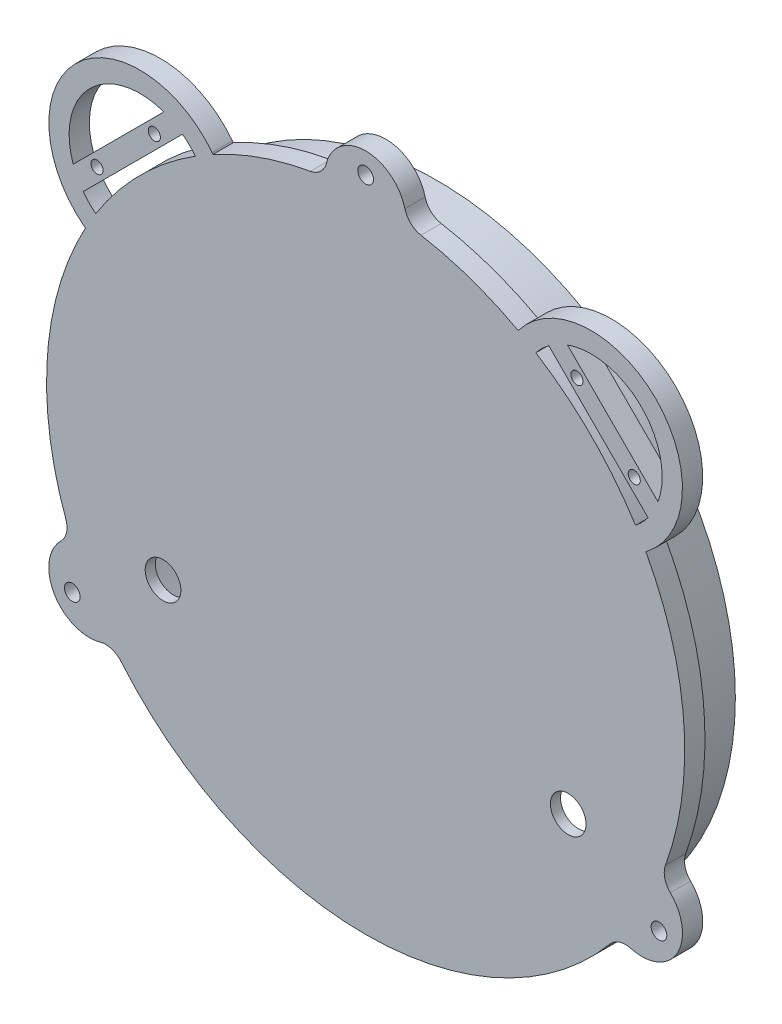
SolidWorks part; units mm, degrees
material "6061 Alloy"
ref_plane "Front Plane" through (0, 0, 0) normal (0, 0, 1) x (1, 0, 0)
ref_plane "Top Plane" through (0, 0, 0) normal (0, 1, 0) x (1, 0, 0)
ref_plane "Right Plane" through (0, 0, 0) normal (1, 0, 0) x (0, 0, -1)
sketch "Sketch1" plane through (0, 0, 0) normal (0, 0, 1) x (1, 0, 0)
  circle A0 centre (0, 0) radius 100.0125
extrude "Extrude1" add sketch "Sketch1" along normal blind 6.35
sketch "Sketch2" plane through (0, 0, 0) normal (0, 0, -1) x (-1, 0, 0)
  circle A0 centre (0, 0) radius 93.6625
extrude "Extrude2" add sketch "Sketch2" along normal blind 15.875
sketch "Sketch3" plane through (0, 0, -15.875) normal (0, 0, -1) x (-1, 0, 0)
  circle A0 centre (0, 0) radius 87.3125
extrude "Cut-Extrude1" cut sketch "Sketch3" against normal blind 19.05
sketch "Sketch5" plane through (0, 0, 6.35) normal (0, 0, 1) x (1, 0, 0)
  circle A18 centre (-63.5, -35.56) radius 5.588
  circle A19 centre (63.5, -35.56) radius 5.588
  dimension "D1" = 63.5
  dimension "D5" = 35.56
  dimension "D2" = 63.5
  dimension "D6" = 35.56
sketch "Sketch7" plane through (0, 0, 6.35) normal (0, 0, 1) x (1, 0, 0)
  line L0 (0, 0) -> (0, 100.0125) construction
  circle A0 centre (0, 0) radius 100.0125 construction
sketch "Sketch8" plane through (0, 0, 6.35) normal (0, 0, 1) x (1, 0, 0)
  line L0 (0, 0) -> (86.6134, -50.0063) construction
  line L1 (0, 0) -> (-86.6134, -50.0063) construction
  line L2 (0, 0) -> (0, 100.0125) construction
  circle A0 centre (0, 0) radius 100.0125 construction
  arc A1 (-12.6744, 99.2062) -> (12.6744, 99.2062) centre (0, 100.0125) cw
  arc A2 (92.2522, -38.6267) -> (79.5779, -60.5794) centre (86.6134, -50.0063) cw
  arc A3 (-92.2522, -38.6267) -> (-79.5779, -60.5794) centre (-86.6134, -50.0063) ccw
  arc A4 (-12.6744, 99.2062) -> (12.6744, 99.2062) centre (0, 0) cw
  arc A5 (92.2522, -38.6267) -> (79.5779, -60.5794) centre (0, 0) cw
  arc A6 (-92.2522, -38.6267) -> (-79.5779, -60.5794) centre (0, 0) ccw
  dimension "D1" = 12.7
  dimension "D2" = 12.7
  dimension "D3" = 12.7
  dimension "D4" = 120
  dimension "D5" = 120
extrude "Extrude3" add sketch "Sketch8" against normal up to surface (6.35 mm away) up to face at (100.0125, 0, 0)
sketch "Sketch10" plane through (0, 0, 6.35) normal (0, 0, 1) x (1, 0, 0)
  line L0 (0, 0) -> (0, 123.4907) construction
  line L1 (0, 0) -> (137.3268, -79.2857) construction
  line L2 (0, 0) -> (-146.5837, -84.6301) construction
extrude "Cut-Extrude2" cut sketch "Sketch5" against normal through all
hole_wizard "#10 (0.1935) Diameter Hole1" positions "3DSketch2" profile "Sketch11" hole size "#10" standard "Ansi Inch"
sketch3d "3DSketch2"
  line L0 (0, 0, 6.35) -> (0, 123.4907, 6.35) construction
  line L1 (0, 0, 6.35) -> (137.3268, -79.2857, 6.35) construction
  line L2 (0, 0, 6.35) -> (-146.5837, -84.6301, 6.35) construction
  point P0 (0, 106.1728, 6.35)
  point P4 (91.9483, -53.0864, 6.35)
  point P8 (-91.9483, -53.0864, 6.35)
  dimension "D1" = 106.3625
  dimension "D2" = 106.3625
  dimension "D3" = 106.3625
sketch "Sketch11" plane through (0, 106.1728, 6.35) normal (1, 0, 0) x (0, -1, 0)
  line L0 (0, 0) -> (0, 331.6766)
  line L1 (0, 331.6766) -> (2.4574, 330.2)
  line L2 (2.4574, 330.2) -> (2.4574, 0)
  line L5 (2.4574, 0) -> (0, 0)
  line L10 (0, 331.6766) -> (-2.4575, 330.2) construction
  line L11 (0, -6.35) -> (0, 107.95) construction
  dimension "Hole Dia." = 4.9149
  dimension "Hole Depth" = 330.2
  dimension "Drill Angle" = 118
hole_wizard "1/8 NPT Tapped Hole1"
sketch3d "3DSketch6"
  line L0 (0, 0, 0) -> (87.3125, 0, 0) construction
  line L2 (0, 0, 0) -> (0, 87.3125, 0) construction
  circle A0 centre (0, 0, 3.175) radius 87.3125 construction
  point P3 (-50.7007, 50.7007, 3.175)
  point P10 (0, 0, -84.1375)
  dimension "D1" = 50.8
  dimension "D2" = 50.8
sketch "Sketch16" plane through (-50.7007, 50.7007, 3.175) normal (1, 0, 0) x (0, 1, 0)
  line L0 (0, 0) -> (0, 13.7095)
  line L1 (4.2164, 11.176) -> (0, 13.7095)
  line L2 (-4.2164, 11.176) -> (0, 13.7095) construction
  line L3 (4.2164, 11.176) -> (4.2164, 6.35)
  line L4 (4.2164, 6.35) -> (4.9362, 6.35)
  line L5 (4.9362, 6.35) -> (5.1263, 0)
  line L6 (-4.9362, 6.35) -> (-5.1263, 0) construction
  line L7 (5.1263, 0) -> (0, 0)
  line L8 (0, -6.35) -> (0, 107.95) construction
  line L11 (-4.2164, 6.35) -> (-4.9362, 6.35) construction
  dimension "Tap Drill Dia." = 8.4328
  dimension "Tap Drill Depth" = 11.176
  dimension "Thread Dia." = 10.2526
  dimension "Thread Angle" = 3.43
  dimension "Thread Depth" = 6.35
  dimension "Drill Angle" = 118
fillet "Fillet1" radius 6.35 6 edges at (92.2522, -38.6267, 3.175) (79.5779, -60.5794, 3.175) (-12.6744, 99.2062, 3.175) (12.6744, 99.2062, 3.175) (-79.5779, -60.5794, 3.175) (-92.2522, -38.6267, 3.175)
sketch "Sketch22" plane through (0, 0, 6.35) normal (0, 0, 1) x (1, 0, 0)
  line L0 (0, 0) -> (0, 100.0125) construction
  line L1 (-79.302, 60.94) -> (-70.3475, 69.946)
  line L2 (-70.9217, 70.5168) -> (0, 0) construction
  line L3 (0, 0) -> (-96.8054, -25.1239) construction
  line L4 (-70.3475, 69.946) -> (-61.393, 78.9519)
  line L5 (-99.2121, -12.6278) -> (-96.0218, -24.9205)
  line L6 (-96.0218, -24.9205) -> (-92.8314, -37.2133)
  line L7 (-79.302, 60.94) -> (-84.7318, 66.3388)
  line L8 (-66.8227, 84.3506) -> (-61.393, 78.9519)
  line L9 (-84.7318, 66.3388) -> (-66.8227, 84.3506)
  line L10 (-92.8314, -37.2133) -> (-99.2121, -38.8693)
  line L11 (-99.2121, -38.8693) -> (-105.5928, -14.2838)
  line L12 (-105.5928, -14.2838) -> (-99.2121, -12.6278)
  line L13 (105.5928, -14.2838) -> (99.2121, -12.6278)
  line L14 (99.2121, -38.8693) -> (105.5928, -14.2838)
  line L15 (92.8314, -37.2133) -> (99.2121, -38.8693)
  line L16 (84.7318, 66.3388) -> (66.8227, 84.3506)
  line L17 (66.8227, 84.3506) -> (61.393, 78.9519)
  line L18 (79.302, 60.94) -> (84.7318, 66.3388)
  line L19 (96.0218, -24.9205) -> (92.8314, -37.2133)
  line L20 (99.2121, -12.6278) -> (96.0218, -24.9205)
  line L21 (70.3475, 69.946) -> (61.393, 78.9519)
  line L22 (79.302, 60.94) -> (70.3475, 69.946)
  circle A0 centre (0, 0) radius 100.0125 construction
  dimension "D1" = 45.164
  dimension "D2" = 104.549
  dimension "D3" = 25.4
  dimension "D4" = 25.4
  dimension "D5" = 12.7
  dimension "D6" = 12.7
extrude "Cut-Extrude5" [suppressed] cut sketch "Sketch22" against normal through all
hole_wizard "Tap Drill for #6 Tap2" [suppressed] positions "3DSketch11" profile "Sketch23" hole size "#6-32" standard "Ansi Inch"
sketch3d "3DSketch11" [suppressed]
  line L0 (61.393, 78.9519, 3.175) -> (79.302, 60.94, 3.175) construction
  line L1 (61.393, 78.9519, 0) -> (61.393, 78.9519, 6.35) construction
  line L2 (79.302, 60.94, 0) -> (79.302, 60.94, 6.35) construction
  line L4 (99.2121, -12.6278, 3.175) -> (92.8314, -37.2133, 3.175) construction
  line L5 (99.2121, -12.6278, 0) -> (99.2121, -12.6278, 6.35) construction
  line L6 (92.8314, -37.2133, 0) -> (92.8314, -37.2133, 6.35) construction
  line L8 (-92.8314, -37.2133, 3.175) -> (-99.2121, -12.6278, 3.175) construction
  line L9 (-92.8314, -37.2133, 0) -> (-92.8314, -37.2133, 6.35) construction
  line L10 (-99.2121, -12.6278, 0) -> (-99.2121, -12.6278, 6.35) construction
  line L12 (-61.393, 78.9519, 3.175) -> (-79.302, 60.94, 3.175) construction
  line L13 (-61.393, 78.9519, 0) -> (-61.393, 78.9519, 6.35) construction
  line L14 (-79.302, 60.94, 0) -> (-79.302, 60.94, 6.35) construction
  line L16 (-96.0218, -24.9205, 6.35) -> (-96.0218, -24.9205, 0) construction
  line L17 (-92.8314, -37.2133, 6.35) -> (-99.2121, -12.6278, 6.35) construction
  line L18 (-92.8314, -37.2133, 0) -> (-99.2121, -12.6278, 0) construction
  line L20 (-70.3475, 69.946, 6.35) -> (-70.3475, 69.946, 0) construction
  line L21 (-79.302, 60.94, 6.35) -> (-61.393, 78.9519, 6.35) construction
  line L22 (-79.302, 60.94, 0) -> (-61.393, 78.9519, 0) construction
  line L24 (70.3475, 69.946, 6.35) -> (70.3475, 69.946, 0) construction
  line L25 (61.393, 78.9519, 6.35) -> (79.302, 60.94, 6.35) construction
  line L26 (61.393, 78.9519, 0) -> (79.302, 60.94, 0) construction
  line L28 (96.0218, -24.9205, 6.35) -> (96.0218, -24.9205, 0) construction
  line L29 (99.2121, -12.6278, 6.35) -> (92.8314, -37.2133, 6.35) construction
  line L30 (99.2121, -12.6278, 0) -> (92.8314, -37.2133, 0) construction
  point P0 (-93.8284, -33.3718, 3.175)
  point P2 (-98.2151, -16.4693, 3.175)
  point P4 (-76.5038, 63.7544, 3.175)
  point P6 (-64.1913, 76.1375, 3.175)
  point P8 (64.1913, 76.1375, 3.175)
  point P10 (76.5038, 63.7544, 3.175)
  point P12 (98.2151, -16.4693, 3.175)
  point P14 (93.8284, -33.3718, 3.175)
  dimension "D1" = 17.4625
  dimension "D2" = 8.7312
  dimension "D3" = 17.4625
  dimension "D4" = 8.7312
  dimension "D5" = 17.4625
  dimension "D6" = 8.7312
  dimension "D7" = 17.4625
  dimension "D8" = 8.7312
sketch "Sketch23" plane through (-93.8284, -33.3718, 3.175) normal (0, 0, 1) x (0.2512, -0.9679, 0)
  line L0 (0, 0) -> (0, 10.3377)
  line L1 (0, 10.3377) -> (1.3525, 9.525)
  line L2 (1.3525, 9.525) -> (1.3525, 0)
  line L5 (1.3525, 0) -> (0, 0)
  line L10 (0, 10.3377) -> (-1.3526, 9.525) construction
  line L11 (0, -6.35) -> (0, 107.95) construction
  dimension "Hole Dia." = 2.7051
  dimension "Hole Depth" = 9.525
  dimension "Drill Angle" = 118
sketch "Sketch24" plane through (0, 0, 3.175) normal (0, 0, -1) x (-1, 0, 0)
  line L0 (0, 0) -> (0, 69.85) construction
  line L1 (44.45, 12.7) -> (-44.45, 12.7) construction
  line L2 (29.5275, 76.8322) -> (-29.5275, 76.8322) construction
  line L3 (29.5275, 76.8322) -> (29.5275, 62.8678) construction
  line L4 (29.5275, 62.8678) -> (-29.5275, 62.8678) construction
  line L5 (-29.5275, 76.8322) -> (-29.5275, 62.8678) construction
  line L6 (29.5275, 76.8322) -> (-29.5275, 62.8678) construction
  line L7 (29.5275, 62.8678) -> (-29.5275, 76.8322) construction
  line L8 (0, 0) -> (0, -100.0125) construction
  line L9 (-60.325, 29.5275) -> (-28.575, 29.5275) construction
  line L10 (-60.325, 29.5275) -> (-60.325, -4.1275) construction
  line L11 (-60.325, -4.1275) -> (-28.575, -4.1275) construction
  line L12 (-28.575, 29.5275) -> (-28.575, -4.1275) construction
  line L13 (-60.325, 29.5275) -> (-28.575, -4.1275) construction
  line L14 (-60.325, -4.1275) -> (-28.575, 29.5275) construction
  line L15 (-34.925, -53.975) -> (34.925, -53.975) construction
  line L16 (60.325, -4.1275) -> (28.575, 29.5275) construction
  line L17 (60.325, 29.5275) -> (28.575, -4.1275) construction
  line L18 (28.575, 29.5275) -> (28.575, -4.1275) construction
  line L19 (60.325, -4.1275) -> (28.575, -4.1275) construction
  line L20 (60.325, 29.5275) -> (60.325, -4.1275) construction
  line L21 (60.325, 29.5275) -> (28.575, 29.5275) construction
  line L22 (0, -25.4) -> (-44.45, -25.4) construction
  circle A0 centre (0, 69.85) radius 15.1765
  circle A1 centre (-60.325, -4.1275) radius 14.4145
  circle A2 centre (-28.575, 29.5275) radius 14.4145
  circle A3 centre (-28.575, -4.1275) radius 14.4145
  circle A4 centre (-60.325, 29.5275) radius 14.4145
  arc A5 (-76.6251, -64.2736) -> (76.6251, -64.2736) centre (0, 0) ccw construction
  circle A6 centre (-34.925, -53.975) radius 19.9644
  circle A7 centre (34.925, -53.975) radius 19.9644
  circle A8 centre (60.325, 29.5275) radius 14.4145
  circle A9 centre (28.575, -4.1275) radius 14.4145
  circle A10 centre (28.575, 29.5275) radius 14.4145
  circle A11 centre (60.325, -4.1275) radius 14.4145
  circle A12 centre (0, 39.6875) radius 12.827
  circle A13 centre (0, 12.7) radius 12.827
  circle A14 centre (0, -14.2875) radius 12.827
  circle A15 centre (0, -41.275) radius 12.827
  circle A16 centre (-29.5275, 62.8678) radius 12.827
  circle A17 centre (29.5275, 62.8678) radius 12.827
  circle A18 centre (0, -69.85) radius 13.6144
  circle A19 centre (-44.45, -25.4) radius 6.8542
  point P31 (0, 12.7)
  dimension "D1" = 30.353
  dimension "D4" = 28.829
  dimension "D5" = 28.829
  dimension "D6" = 28.829
  dimension "D8" = 28.829
  dimension "D11" = 39.9288
  dimension "D12" = 39.9288
  dimension "D15" = 25.654
  dimension "D17" = 25.654
  dimension "D18" = 26.9875
  dimension "D19" = 25.654
  dimension "D21" = 25.654
  dimension "D23" = 25.654
  dimension "D25" = 25.654
  dimension "D26" = 27.2288
  dimension "D27" = 28.575
  dimension "D29" = 13.7084
  dimension "D2" = 69.85
  dimension "D3" = 44.45
  dimension "D7" = 31.75
  dimension "D9" = 12.7
  dimension "D10" = 33.655
  dimension "D13" = 34.925
  dimension "D14" = 34.925
  dimension "D16" = 39.6875
  dimension "D20" = 26.9875
  dimension "D22" = 26.9875
  dimension "D24" = 59.055
  dimension "D28" = 53.975
  dimension "D30" = 25.4
  dimension "D31" = 44.45
sketch "Sketch25" plane through (0, 0, 6.35) normal (0, 0, 1) x (1, 0, 0)
  line L0 (0, 0) -> (-70.7195, 70.7195) construction
  line L1 (0, 0) -> (70.7195, 70.7195) construction
  line L2 (0, 0) -> (0, 100.0125) construction
  arc A0 (-17.35, 98.4961) -> (-93.9751, -34.2225) centre (0, 0) ccw construction
  arc A1 (93.9751, -34.2225) -> (17.35, 98.4961) centre (0, 0) ccw construction
  arc A2 (-86.2539, 50.6237) -> (-50.6237, 86.2539) centre (-70.7195, 70.7195) cw construction
  arc A3 (-84.3121, 53.1357) -> (-53.1357, 84.3121) centre (-70.7195, 70.7195) cw
  arc A4 (-88.1957, 48.1117) -> (-48.1117, 88.1957) centre (-70.7195, 70.7195) cw
  arc A5 (-84.3121, 53.1357) -> (-88.1957, 48.1117) centre (-86.2539, 50.6237) cw
  arc A6 (-53.1357, 84.3121) -> (-48.1117, 88.1957) centre (-50.6237, 86.2539) ccw
  dimension "D1" = 25.4
  dimension "D2" = 3.175
  dimension "D3" = 3.175
extrude "Boss-Extrude1" add sketch "Sketch25" against normal blind 6.35
sketch "Sketch26" plane through (0, 0, 6.35) normal (0, 0, 1) x (1, 0, 0)
  line L0 (-90.9251, 90.9251) -> (-70.7195, 70.7195) construction
  line L1 (-93.1702, 61.7393) -> (-61.7393, 93.1702)
  line L2 (-61.7393, 93.1702) -> (-57.2491, 88.68)
  line L3 (-57.2491, 88.68) -> (-88.68, 57.2491)
  line L4 (-88.68, 57.2491) -> (-93.1702, 61.7393)
  arc A0 (-48.1117, 88.1957) -> (-88.1957, 48.1117) centre (-70.7195, 70.7195) ccw construction
  arc A1 (-53.3552, 84.5915) -> (-84.5915, 53.3552) centre (0, 0) ccw construction
  point P10 (0, 0)
  dimension "D3" = 3.175
  dimension "D1" = 44.45
  dimension "D2" = 6.35
extrude "Boss-Extrude2" add sketch "Sketch26" against normal blind 6.35
hole_wizard "#6 Clearance Hole1" positions "Sketch28" profile "Sketch27" hole size "#6" standard "Ansi Inch"
sketch "Sketch28" plane through (0, 0, 6.35) normal (0, 0, 1) x (1, 0, 0)
  line L0 (-91.6537, 63.2557) -> (-86.8606, 59.0686) construction
  line L1 (-88.5188, 57.4103) -> (-57.4103, 88.5188) construction
  line L2 (-86.8606, 59.0686) -> (-89.2571, 61.1621) construction
  line L4 (-63.2557, 91.6537) -> (-58.7655, 87.1636) construction
  line L6 (-89.2571, 61.1621) -> (-61.0106, 89.4087) construction
  line L8 (-77.4547, 77.4547) -> (-72.9646, 72.9646) construction
  line L9 (-63.2557, 91.6537) -> (-91.6537, 63.2557) construction
  point P0 (-84.1899, 66.2294)
  point P1 (-66.2294, 84.1899)
  dimension "D1" = 12.7
  dimension "D2" = 12.7
sketch "Sketch27" plane through (-84.1899, 66.2294, 6.35) normal (1, 0, 0) x (0, -1, 0)
  line L0 (0, 0) -> (0, 26.5408)
  line L1 (0, 26.5408) -> (1.8986, 25.4)
  line L2 (1.8986, 25.4) -> (1.8986, 0)
  line L5 (1.8986, 0) -> (0, 0)
  line L10 (0, 26.5408) -> (-1.8986, 25.4) construction
  line L11 (0, -6.35) -> (0, 107.95) construction
  dimension "Hole Dia." = 3.7973
  dimension "Hole Depth" = 25.4
  dimension "Drill Angle" = 118
mirror "Mirror1" about plane through (0, 0, 0) normal (1, 0, 0) of "#6 Clearance Hole1", "Boss-Extrude2", "Boss-Extrude1"
